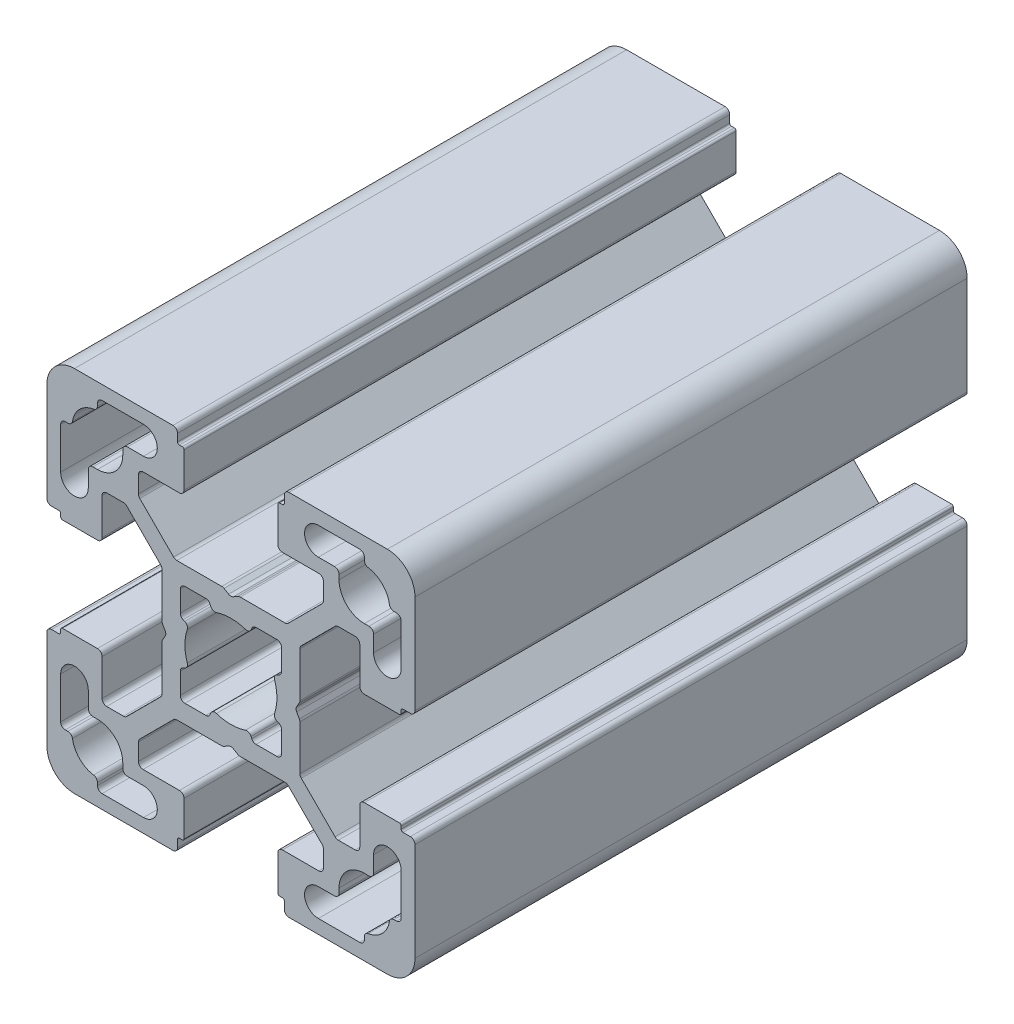
SolidWorks part; units mm, degrees
material "1060 Сплав"
ref_plane "Спереди" through (0, 0, 0) normal (0, 0, 1) x (1, 0, 0)
ref_plane "Сверху" through (0, 0, 0) normal (0, 1, 0) x (1, 0, 0)
ref_plane "Справа" through (0, 0, 0) normal (1, 0, 0) x (0, 0, -1)
sketch "Эскиз1" plane through (0, 0, 0) normal (0, 0, 1) x (1, 0, 0)
  line L0 (-14.5, 18) -> (-14.5, 17.7113)
  line L1 (-18.5, -5.6) -> (-18.5, -5.3)
  line L3 (-14, 18.5) -> (-9.5, 18.5)
  line L4 (18.5, 5.6) -> (18.5, 5.3)
  line L5 (0.25, 7.1443) -> (0.75, 7.433)
  line L6 (1, 7.5) -> (5.8787, 7.5)
  line L7 (5.6, 14) -> (5.6255, 13.9844)
  line L8 (-0.25, 7.1443) -> (-0.75, 7.433)
  line L9 (-5.8787, 7.5) -> (-1, 7.5)
  line L10 (-7.5, 5.8787) -> (-7.5, 1)
  line L11 (-5.6, 18.5) -> (-5.3, 18.5)
  line L12 (10.05, 13.5) -> (10.05, 11.6713)
  line L13 (-14, 5.6) -> (-13.9844, 5.6255)
  line L14 (-13.5, 10.05) -> (-11.6713, 10.05)
  line L15 (-5.1994, 2.2693) -> (-5.0205, 2.1915)
  line L16 (-19.5, 5.8) -> (-18.7, 5.8)
  line L17 (-18.3, 5.1) -> (-14.5, 5.1)
  line L18 (-14, 9.55) -> (-14, 5.6)
  line L19 (-7.6464, 6.2322) -> (-11.3178, 9.9036)
  line L20 (-20, 6.3) -> (-20, 17)
  line L21 (5.1994, -2.2693) -> (5.0205, -2.1915)
  line L22 (-14.5, 18) -> (-14.5, 17.7113)
  line L23 (-14, 18.5) -> (-9.5, 18.5)
  line L24 (-9.5, 15.5) -> (-11.25, 15.5)
  line L25 (-11.75, 15) -> (-11.75, 14.5)
  line L26 (-15, 11.75) -> (-14.5, 11.75)
  line L27 (-15.5, 9.5) -> (-15.5, 11.25)
  line L28 (-18.5, 14) -> (-18.5, 9.5)
  line L29 (-18, 14.5) -> (-17.7113, 14.5)
  line L30 (2.7278, -5.5) -> (5, -5.5)
  line L31 (-2.7278, 5.5) -> (-5, 5.5)
  line L32 (-5.5, 2.7278) -> (-5.5, 5)
  line L33 (5.8, 19.5) -> (5.8, 18.7)
  line L34 (5.1, 18.3) -> (5.1, 14.5)
  line L35 (-2.2693, 5.1994) -> (-2.1915, 5.0205)
  line L36 (9.55, 14) -> (5.6, 14)
  line L37 (-9.5, 15.5) -> (-11.25, 15.5)
  line L38 (2.2693, 5.1994) -> (2.1915, 5.0205)
  line L39 (5.5, 2.7278) -> (5.5, 5)
  line L40 (2.7278, 5.5) -> (5, 5.5)
  line L41 (5.1994, 2.2693) -> (5.0205, 2.1915)
  line L42 (5.5, -2.7278) -> (5.5, -5)
  line L43 (2.2693, -5.1994) -> (2.1915, -5.0205)
  line L44 (-2.2693, -5.1994) -> (-2.1915, -5.0205)
  line L45 (-5.5, -2.7278) -> (-5.5, -5)
  line L46 (-2.7278, -5.5) -> (-5, -5.5)
  line L47 (-5.1994, -2.2693) -> (-5.0205, -2.1915)
  line L48 (-7.1443, 0.25) -> (-7.433, 0.75)
  line L49 (-7.5, -1) -> (-7.5, -5.8787)
  line L50 (-7.1443, -0.25) -> (-7.433, -0.75)
  line L51 (-11.75, 15) -> (-11.75, 14.5)
  line L52 (-15, 11.75) -> (-14.5, 11.75)
  line L53 (-15.5, 9.5) -> (-15.5, 11.25)
  line L54 (-6.3, 20) -> (-17, 20)
  line L55 (-6.2322, 7.6464) -> (-9.9036, 11.3178)
  line L56 (-9.55, 14) -> (-5.6, 14)
  line L57 (-5.1, 18.3) -> (-5.1, 14.5)
  line L58 (-5.8, 19.5) -> (-5.8, 18.7)
  line L59 (-10.05, 13.5) -> (-10.05, 11.6713)
  line L60 (-5.6, 14) -> (-5.6255, 13.9844)
  line L61 (6.2322, 7.6464) -> (9.9036, 11.3178)
  line L62 (6.2322, 7.6464) -> (9.9036, 11.3178)
  line L63 (6.3, 20) -> (17, 20)
  line L64 (15.5, 9.5) -> (15.5, 11.25)
  line L65 (15, 11.75) -> (14.5, 11.75)
  line L66 (11.75, 15) -> (11.75, 14.5)
  line L67 (7.1443, -0.25) -> (7.433, -0.75)
  line L68 (7.5, -1) -> (7.5, -5.8787)
  line L69 (7.1443, 0.25) -> (7.433, 0.75)
  line L70 (5.1994, -2.2693) -> (5.0205, -2.1915)
  line L71 (2.7278, -5.5) -> (5, -5.5)
  line L72 (5.5, -2.7278) -> (5.5, -5)
  line L73 (2.2693, -5.1994) -> (2.1915, -5.0205)
  line L74 (9.5, 15.5) -> (11.25, 15.5)
  line L75 (2.2693, 5.1994) -> (2.1915, 5.0205)
  line L76 (5.5, 2.7278) -> (5.5, 5)
  line L77 (2.7278, 5.5) -> (5, 5.5)
  line L78 (18, 14.5) -> (17.7113, 14.5)
  line L79 (18.5, 14) -> (18.5, 9.5)
  line L80 (15.5, 9.5) -> (15.5, 11.25)
  line L81 (15, 11.75) -> (14.5, 11.75)
  line L82 (11.75, 15) -> (11.75, 14.5)
  line L83 (9.5, 15.5) -> (11.25, 15.5)
  line L84 (14, 18.5) -> (9.5, 18.5)
  line L85 (14.5, 18) -> (14.5, 17.7113)
  line L86 (20, 6.3) -> (20, 17)
  line L87 (7.6464, 6.2322) -> (11.3178, 9.9036)
  line L88 (7.6464, 6.2322) -> (11.3178, 9.9036)
  line L89 (14, 9.55) -> (14, 5.6)
  line L90 (18.3, 5.1) -> (14.5, 5.1)
  line L91 (5.1994, 2.2693) -> (5.0205, 2.1915)
  line L92 (19.5, 5.8) -> (18.7, 5.8)
  line L93 (13.5, 10.05) -> (11.6713, 10.05)
  line L94 (7.5, 5.8787) -> (7.5, 1)
  line L95 (14, 5.6) -> (13.9844, 5.6255)
  line L96 (5.6, 18.5) -> (5.3, 18.5)
  line L97 (5.1994, -2.2693) -> (5.0205, -2.1915)
  line L98 (14, 18.5) -> (9.5, 18.5)
  line L99 (14.5, 18) -> (14.5, 17.7113)
  line L100 (14.5, -18) -> (14.5, -17.7113)
  line L101 (7.6464, -6.2322) -> (11.3178, -9.9036)
  line L102 (14, -18.5) -> (9.5, -18.5)
  line L103 (5.6, -18.5) -> (5.3, -18.5)
  line L104 (14, -5.6) -> (13.9844, -5.6255)
  line L105 (13.5, -10.05) -> (11.6713, -10.05)
  line L106 (19.5, -5.8) -> (18.7, -5.8)
  line L107 (5.1994, -2.2693) -> (5.0205, -2.1915)
  line L108 (18.3, -5.1) -> (14.5, -5.1)
  line L109 (14, -9.55) -> (14, -5.6)
  line L110 (7.6464, -6.2322) -> (11.3178, -9.9036)
  line L111 (2.7278, -5.5) -> (5, -5.5)
  line L112 (5.5, -2.7278) -> (5.5, -5)
  line L113 (2.2693, -5.1994) -> (2.1915, -5.0205)
  line L114 (7.6464, -6.2322) -> (11.3178, -9.9036)
  line L115 (20, -6.3) -> (20, -17)
  line L116 (14.5, -18) -> (14.5, -17.7113)
  line L117 (14, -18.5) -> (9.5, -18.5)
  line L118 (9.5, -15.5) -> (11.25, -15.5)
  line L119 (6.2322, -7.6464) -> (9.9036, -11.3178)
  line L120 (11.75, -15) -> (11.75, -14.5)
  line L121 (15, -11.75) -> (14.5, -11.75)
  line L122 (15.5, -9.5) -> (15.5, -11.25)
  line L123 (18.5, -14) -> (18.5, -9.5)
  line L124 (18, -14.5) -> (17.7113, -14.5)
  line L125 (2.7278, -5.5) -> (5, -5.5)
  line L126 (-6.2322, -7.6464) -> (-9.9036, -11.3178)
  line L127 (5.5, -2.7278) -> (5.5, -5)
  line L128 (2.2693, -5.1994) -> (2.1915, -5.0205)
  line L129 (9.5, -15.5) -> (11.25, -15.5)
  line L130 (11.75, -15) -> (11.75, -14.5)
  line L131 (5.1994, -2.2693) -> (5.0205, -2.1915)
  line L132 (2.7278, -5.5) -> (5, -5.5)
  line L133 (5.5, -2.7278) -> (5.5, -5)
  line L134 (2.2693, -5.1994) -> (2.1915, -5.0205)
  line L135 (15, -11.75) -> (14.5, -11.75)
  line L136 (-2.2693, -5.1994) -> (-2.1915, -5.0205)
  line L137 (15.5, -9.5) -> (15.5, -11.25)
  line L138 (6.3, -20) -> (17, -20)
  line L139 (-5.5, -2.7278) -> (-5.5, -5)
  line L140 (-2.7278, -5.5) -> (-5, -5.5)
  line L141 (6.2322, -7.6464) -> (9.9036, -11.3178)
  line L142 (6.2322, -7.6464) -> (9.9036, -11.3178)
  line L143 (-5.6, -14) -> (-5.6255, -13.9844)
  line L144 (-10.05, -13.5) -> (-10.05, -11.6713)
  line L145 (-5.8, -19.5) -> (-5.8, -18.7)
  line L146 (-5.1, -18.3) -> (-5.1, -14.5)
  line L147 (-9.55, -14) -> (-5.6, -14)
  line L148 (-6.2322, -7.6464) -> (-9.9036, -11.3178)
  line L149 (-6.3, -20) -> (-17, -20)
  line L150 (-7.6464, -6.2322) -> (-11.3178, -9.9036)
  line L151 (-15.5, -9.5) -> (-15.5, -11.25)
  line L152 (-15, -11.75) -> (-14.5, -11.75)
  line L153 (-11.75, -15) -> (-11.75, -14.5)
  line L154 (-5.1994, -2.2693) -> (-5.0205, -2.1915)
  line L155 (-13.5, -10.05) -> (-11.6713, -10.05)
  line L156 (5.1994, -2.2693) -> (5.0205, -2.1915)
  line L157 (2.7278, -5.5) -> (5, -5.5)
  line L158 (-5.8787, -7.5) -> (-1, -7.5)
  line L159 (-0.25, -7.1443) -> (-0.75, -7.433)
  line L160 (5.5, -2.7278) -> (5.5, -5)
  line L161 (1, -7.5) -> (5.8787, -7.5)
  line L162 (0.25, -7.1443) -> (0.75, -7.433)
  line L163 (2.2693, -5.1994) -> (2.1915, -5.0205)
  line L164 (-9.5, -15.5) -> (-11.25, -15.5)
  line L165 (9.55, -14) -> (5.6, -14)
  line L166 (-18.5, 5.6) -> (-18.5, 5.3)
  line L167 (-2.2693, -5.1994) -> (-2.1915, -5.0205)
  line L168 (5.1, -18.3) -> (5.1, -14.5)
  line L169 (5.8, -19.5) -> (5.8, -18.7)
  line L170 (-5.5, -2.7278) -> (-5.5, -5)
  line L171 (-2.7278, -5.5) -> (-5, -5.5)
  line L172 (-18, -14.5) -> (-17.7113, -14.5)
  line L173 (-18.5, -14) -> (-18.5, -9.5)
  line L174 (-15.5, -9.5) -> (-15.5, -11.25)
  line L175 (-15, -11.75) -> (-14.5, -11.75)
  line L176 (-11.75, -15) -> (-11.75, -14.5)
  line L177 (-9.5, -15.5) -> (-11.25, -15.5)
  line L178 (-14, -18.5) -> (-9.5, -18.5)
  line L179 (-14.5, -18) -> (-14.5, -17.7113)
  line L180 (-20, -6.3) -> (-20, -17)
  line L181 (-7.6464, -6.2322) -> (-11.3178, -9.9036)
  line L182 (-14, -9.55) -> (-14, -5.6)
  line L183 (-18.3, -5.1) -> (-14.5, -5.1)
  line L184 (-19.5, -5.8) -> (-18.7, -5.8)
  line L185 (-5.1994, -2.2693) -> (-5.0205, -2.1915)
  line L186 (-13.5, -10.05) -> (-11.6713, -10.05)
  line L187 (-14, -5.6) -> (-13.9844, -5.6255)
  line L188 (10.05, -13.5) -> (10.05, -11.6713)
  line L189 (-5.6, -18.5) -> (-5.3, -18.5)
  line L190 (-5.8787, -7.5) -> (-1, -7.5)
  line L191 (-0.25, -7.1443) -> (-0.75, -7.433)
  line L192 (5.6, -14) -> (5.6255, -13.9844)
  line L193 (1, -7.5) -> (5.8787, -7.5)
  line L194 (0.25, -7.1443) -> (0.75, -7.433)
  line L195 (18.5, -5.6) -> (18.5, -5.3)
  line L196 (-14, -18.5) -> (-9.5, -18.5)
  line L197 (-14.5, -18) -> (-14.5, -17.7113)
  arc A0 (-17, 20) -> (-20, 17) centre (-17, 17) ccw
  arc A1 (-4.7453, 1.5754) -> (-4.7453, -1.5754) centre (0, 0) ccw
  arc A2 (-9.5, 15.5) -> (-9.5, 18.5) centre (-9.5, 17) ccw
  arc A3 (-14.9231, 17.2173) -> (-17.2173, 14.9231) centre (-14.5, 14.5) ccw
  arc A4 (-14.5, 11.75) -> (-11.75, 14.5) centre (-14.5, 14.5) ccw
  arc A5 (-15.5, 9.5) -> (-18.5, 9.5) centre (-17, 9.5) cw
  arc A6 (-11.3178, 9.9036) -> (-11.6713, 10.05) centre (-11.6713, 9.55) ccw
  arc A7 (-13.5, 10.05) -> (-14, 9.55) centre (-13.5, 9.55) ccw
  arc A8 (-14.5, 5.1) -> (-14, 5.6) centre (-14.5, 5.6) ccw
  arc A9 (-20, 6.3) -> (-19.5, 5.8) centre (-19.5, 6.3) ccw
  arc A10 (-11.25, 15.5) -> (-11.75, 15) centre (-11.25, 15) ccw
  arc A11 (-18.3, 5.1) -> (-18.5, 5.3) centre (-18.3, 5.3) cw
  arc A12 (-18.7, 5.8) -> (-18.5, 5.6) centre (-18.7, 5.6) cw
  arc A13 (-7.6464, 6.2322) -> (-7.5, 5.8787) centre (-8, 5.8787) cw
  arc A14 (-15, 11.75) -> (-15.5, 11.25) centre (-15, 11.25) ccw
  arc A15 (-14.5, 18) -> (-14, 18.5) centre (-14, 18) cw
  arc A16 (-18.5, 14) -> (-18, 14.5) centre (-18, 14) cw
  arc A17 (-14.5, 17.7113) -> (-14.9231, 17.2173) centre (-15, 17.7113) cw
  arc A18 (-17.7113, 14.5) -> (-17.2173, 14.9231) centre (-17.7113, 15) ccw
  arc A19 (-5.0205, 2.1915) -> (-4.7453, 1.5754) centre (-5.2198, 1.733) cw
  arc A20 (-2.1915, 5.0205) -> (-1.5754, 4.7453) centre (-1.733, 5.2198) ccw
  arc A21 (-2.2693, 5.1994) -> (-2.7278, 5.5) centre (-2.7278, 5) ccw
  arc A22 (-5, 5.5) -> (-5.5, 5) centre (-5, 5) ccw
  arc A23 (-5.1994, 2.2693) -> (-5.5, 2.7278) centre (-5, 2.7278) cw
  arc A24 (5.1994, 2.2693) -> (5.5, 2.7278) centre (5, 2.7278) ccw
  arc A25 (5, 5.5) -> (5.5, 5) centre (5, 5) cw
  arc A26 (2.2693, 5.1994) -> (2.7278, 5.5) centre (2.7278, 5) cw
  arc A27 (2.1915, 5.0205) -> (1.5754, 4.7453) centre (1.733, 5.2198) cw
  arc A28 (5.0205, 2.1915) -> (4.7453, 1.5754) centre (5.2198, 1.733) ccw
  arc A29 (5.0205, -2.1915) -> (4.7453, -1.5754) centre (5.2198, -1.733) cw
  arc A30 (2.1915, -5.0205) -> (1.5754, -4.7453) centre (1.733, -5.2198) ccw
  arc A31 (2.2693, -5.1994) -> (2.7278, -5.5) centre (2.7278, -5) ccw
  arc A32 (5, -5.5) -> (5.5, -5) centre (5, -5) ccw
  arc A33 (5.1994, -2.2693) -> (5.5, -2.7278) centre (5, -2.7278) cw
  arc A34 (-5.1994, -2.2693) -> (-5.5, -2.7278) centre (-5, -2.7278) ccw
  arc A35 (-5, -5.5) -> (-5.5, -5) centre (-5, -5) cw
  arc A36 (-2.2693, -5.1994) -> (-2.7278, -5.5) centre (-2.7278, -5) cw
  arc A37 (-2.1915, -5.0205) -> (-1.5754, -4.7453) centre (-1.733, -5.2198) cw
  arc A38 (-5.0205, -2.1915) -> (-4.7453, -1.5754) centre (-5.2198, -1.733) ccw
  arc A39 (1.5754, 4.7453) -> (-1.5754, 4.7453) centre (0, 0) ccw
  arc A40 (4.7453, -1.5754) -> (4.7453, 1.5754) centre (0, 0) ccw
  arc A41 (-1.5754, -4.7453) -> (1.5754, -4.7453) centre (0, 0) ccw
  arc A42 (-7.433, -0.75) -> (-7.5, -1) centre (-7, -1) ccw
  arc A43 (-7.1443, -0.25) -> (-7.1443, 0.25) centre (-7.5774, 0) ccw
  arc A44 (-7.433, 0.75) -> (-7.5, 1) centre (-7, 1) cw
  arc A45 (-14.5, 17.7113) -> (-14.9231, 17.2173) centre (-15, 17.7113) cw
  arc A46 (-17.7113, 14.5) -> (-17.2173, 14.9231) centre (-17.7113, 15) ccw
  arc A47 (-14, 18.5) -> (-14.5, 18) centre (-14, 18) ccw
  arc A48 (-11.75, 15) -> (-11.25, 15.5) centre (-11.25, 15) cw
  arc A49 (-6.2322, 7.6464) -> (-5.8787, 7.5) centre (-5.8787, 8) ccw
  arc A50 (-5.8, 18.7) -> (-5.6, 18.5) centre (-5.6, 18.7) ccw
  arc A51 (-5.1, 18.3) -> (-5.3, 18.5) centre (-5.3, 18.3) ccw
  arc A52 (-15.5, 11.25) -> (-15, 11.75) centre (-15, 11.25) cw
  arc A53 (-6.3, 20) -> (-5.8, 19.5) centre (-6.3, 19.5) cw
  arc A54 (-5.1, 14.5) -> (-5.6, 14) centre (-5.6, 14.5) cw
  arc A55 (-10.05, 13.5) -> (-9.55, 14) centre (-9.55, 13.5) cw
  arc A56 (-9.9036, 11.3178) -> (-10.05, 11.6713) centre (-9.55, 11.6713) cw
  arc A57 (-9.5, 15.5) -> (-9.5, 18.5) centre (-9.5, 17) ccw
  arc A58 (-15.5, 9.5) -> (-18.5, 9.5) centre (-17, 9.5) cw
  arc A59 (-0.75, 7.433) -> (-1, 7.5) centre (-1, 7) ccw
  arc A60 (0.25, 7.1443) -> (-0.25, 7.1443) centre (0, 7.5774) cw
  arc A61 (0.75, 7.433) -> (1, 7.5) centre (1, 7) cw
  arc A62 (15.5, 9.5) -> (18.5, 9.5) centre (17, 9.5) ccw
  arc A63 (9.5, 15.5) -> (9.5, 18.5) centre (9.5, 17) cw
  arc A64 (9.9036, 11.3178) -> (10.05, 11.6713) centre (9.55, 11.6713) ccw
  arc A65 (9.9036, 11.3178) -> (10.05, 11.6713) centre (9.55, 11.6713) ccw
  arc A66 (10.05, 13.5) -> (9.55, 14) centre (9.55, 13.5) ccw
  arc A67 (5.1, 14.5) -> (5.6, 14) centre (5.6, 14.5) ccw
  arc A68 (6.3, 20) -> (5.8, 19.5) centre (6.3, 19.5) ccw
  arc A69 (15.5, 11.25) -> (15, 11.75) centre (15, 11.25) ccw
  arc A70 (5.1, 18.3) -> (5.3, 18.5) centre (5.3, 18.3) cw
  arc A71 (6.2322, 7.6464) -> (5.8787, 7.5) centre (5.8787, 8) cw
  arc A72 (5.8, 18.7) -> (5.6, 18.5) centre (5.6, 18.7) cw
  arc A73 (6.2322, 7.6464) -> (5.8787, 7.5) centre (5.8787, 8) cw
  arc A74 (11.75, 15) -> (11.25, 15.5) centre (11.25, 15) ccw
  arc A75 (14, 18.5) -> (14.5, 18) centre (14, 18) cw
  arc A76 (7.433, 0.75) -> (7.5, 1) centre (7, 1) ccw
  arc A77 (7.1443, -0.25) -> (7.1443, 0.25) centre (7.5774, 0) cw
  arc A78 (7.433, -0.75) -> (7.5, -1) centre (7, -1) cw
  arc A79 (5.0205, -2.1915) -> (4.7453, -1.5754) centre (5.2198, -1.733) cw
  arc A80 (2.2693, -5.1994) -> (2.7278, -5.5) centre (2.7278, -5) ccw
  arc A81 (5, -5.5) -> (5.5, -5) centre (5, -5) ccw
  arc A82 (5.1994, -2.2693) -> (5.5, -2.7278) centre (5, -2.7278) cw
  arc A83 (5.1994, 2.2693) -> (5.5, 2.7278) centre (5, 2.7278) ccw
  arc A84 (5, 5.5) -> (5.5, 5) centre (5, 5) cw
  arc A85 (2.2693, 5.1994) -> (2.7278, 5.5) centre (2.7278, 5) cw
  arc A86 (5.0205, 2.1915) -> (4.7453, 1.5754) centre (5.2198, 1.733) ccw
  arc A87 (17.7113, 14.5) -> (17.2173, 14.9231) centre (17.7113, 15) cw
  arc A88 (14.5, 17.7113) -> (14.9231, 17.2173) centre (15, 17.7113) ccw
  arc A89 (5, 5.5) -> (5.5, 5) centre (5, 5) cw
  arc A90 (17.7113, 14.5) -> (17.2173, 14.9231) centre (17.7113, 15) cw
  arc A91 (14.5, 17.7113) -> (14.9231, 17.2173) centre (15, 17.7113) ccw
  arc A92 (7.6464, 6.2322) -> (7.5, 5.8787) centre (8, 5.8787) ccw
  arc A93 (18.5, 14) -> (18, 14.5) centre (18, 14) ccw
  arc A94 (14.5, 18) -> (14, 18.5) centre (14, 18) ccw
  arc A95 (15, 11.75) -> (15.5, 11.25) centre (15, 11.25) cw
  arc A96 (7.6464, 6.2322) -> (7.5, 5.8787) centre (8, 5.8787) ccw
  arc A97 (18.7, 5.8) -> (18.5, 5.6) centre (18.7, 5.6) ccw
  arc A98 (18.3, 5.1) -> (18.5, 5.3) centre (18.3, 5.3) ccw
  arc A99 (11.3178, 9.9036) -> (11.6713, 10.05) centre (11.6713, 9.55) cw
  arc A100 (11.25, 15.5) -> (11.75, 15) centre (11.25, 15) cw
  arc A101 (20, 6.3) -> (19.5, 5.8) centre (19.5, 6.3) cw
  arc A102 (14.5, 5.1) -> (14, 5.6) centre (14.5, 5.6) cw
  arc A103 (13.5, 10.05) -> (14, 9.55) centre (13.5, 9.55) cw
  arc A104 (4.7453, 1.5754) -> (4.7453, -1.5754) centre (0, 0) cw
  arc A105 (11.3178, 9.9036) -> (11.6713, 10.05) centre (11.6713, 9.55) cw
  arc A106 (15.5, 9.5) -> (18.5, 9.5) centre (17, 9.5) ccw
  arc A107 (14.5, 11.75) -> (11.75, 14.5) centre (14.5, 14.5) cw
  arc A108 (14.9231, 17.2173) -> (17.2173, 14.9231) centre (14.5, 14.5) cw
  arc A109 (9.5, 15.5) -> (9.5, 18.5) centre (9.5, 17) cw
  arc A110 (17, 20) -> (20, 17) centre (17, 17) cw
  arc A111 (11.3178, -9.9036) -> (11.6713, -10.05) centre (11.6713, -9.55) ccw
  arc A112 (17, -20) -> (20, -17) centre (17, -17) ccw
  arc A113 (9.5, -15.5) -> (9.5, -18.5) centre (9.5, -17) ccw
  arc A114 (14.9231, -17.2173) -> (17.2173, -14.9231) centre (14.5, -14.5) ccw
  arc A115 (14.5, -11.75) -> (11.75, -14.5) centre (14.5, -14.5) ccw
  arc A116 (15.5, -9.5) -> (18.5, -9.5) centre (17, -9.5) cw
  arc A117 (11.3178, -9.9036) -> (11.6713, -10.05) centre (11.6713, -9.55) ccw
  arc A118 (7.6464, -6.2322) -> (7.5, -5.8787) centre (8, -5.8787) cw
  arc A119 (13.5, -10.05) -> (14, -9.55) centre (13.5, -9.55) ccw
  arc A120 (14.5, -5.1) -> (14, -5.6) centre (14.5, -5.6) ccw
  arc A121 (20, -6.3) -> (19.5, -5.8) centre (19.5, -6.3) ccw
  arc A122 (11.25, -15.5) -> (11.75, -15) centre (11.25, -15) ccw
  arc A123 (11.3178, -9.9036) -> (11.6713, -10.05) centre (11.6713, -9.55) ccw
  arc A124 (5.0205, -2.1915) -> (4.7453, -1.5754) centre (5.2198, -1.733) cw
  arc A125 (2.2693, -5.1994) -> (2.7278, -5.5) centre (2.7278, -5) ccw
  arc A126 (5, -5.5) -> (5.5, -5) centre (5, -5) ccw
  arc A127 (5.1994, -2.2693) -> (5.5, -2.7278) centre (5, -2.7278) cw
  arc A128 (18.3, -5.1) -> (18.5, -5.3) centre (18.3, -5.3) cw
  arc A129 (18.7, -5.8) -> (18.5, -5.6) centre (18.7, -5.6) cw
  arc A130 (7.6464, -6.2322) -> (7.5, -5.8787) centre (8, -5.8787) cw
  arc A131 (15, -11.75) -> (15.5, -11.25) centre (15, -11.25) ccw
  arc A132 (6.2322, -7.6464) -> (5.8787, -7.5) centre (5.8787, -8) ccw
  arc A133 (14.5, -18) -> (14, -18.5) centre (14, -18) cw
  arc A134 (18.5, -14) -> (18, -14.5) centre (18, -14) cw
  arc A135 (7.6464, -6.2322) -> (7.5, -5.8787) centre (8, -5.8787) cw
  arc A136 (14.5, -17.7113) -> (14.9231, -17.2173) centre (15, -17.7113) cw
  arc A137 (17.7113, -14.5) -> (17.2173, -14.9231) centre (17.7113, -15) ccw
  arc A138 (5, -5.5) -> (5.5, -5) centre (5, -5) ccw
  arc A139 (9.9036, -11.3178) -> (10.05, -11.6713) centre (9.55, -11.6713) cw
  arc A140 (14.5, -17.7113) -> (14.9231, -17.2173) centre (15, -17.7113) cw
  arc A141 (17.7113, -14.5) -> (17.2173, -14.9231) centre (17.7113, -15) ccw
  arc A142 (0.75, -7.433) -> (1, -7.5) centre (1, -7) ccw
  arc A143 (0.25, -7.1443) -> (-0.25, -7.1443) centre (0, -7.5774) ccw
  arc A144 (-0.75, -7.433) -> (-1, -7.5) centre (-1, -7) cw
  arc A145 (2.2693, -5.1994) -> (2.7278, -5.5) centre (2.7278, -5) ccw
  arc A146 (5, -5.5) -> (5.5, -5) centre (5, -5) ccw
  arc A147 (-9.9036, -11.3178) -> (-10.05, -11.6713) centre (-9.55, -11.6713) ccw
  arc A148 (5.1994, -2.2693) -> (5.5, -2.7278) centre (5, -2.7278) cw
  arc A149 (14, -18.5) -> (14.5, -18) centre (14, -18) ccw
  arc A150 (11.75, -15) -> (11.25, -15.5) centre (11.25, -15) cw
  arc A151 (6.2322, -7.6464) -> (5.8787, -7.5) centre (5.8787, -8) ccw
  arc A152 (5.8, -18.7) -> (5.6, -18.5) centre (5.6, -18.7) ccw
  arc A153 (6.2322, -7.6464) -> (5.8787, -7.5) centre (5.8787, -8) ccw
  arc A154 (-6.2322, -7.6464) -> (-5.8787, -7.5) centre (-5.8787, -8) cw
  arc A155 (5.1, -18.3) -> (5.3, -18.5) centre (5.3, -18.3) ccw
  arc A156 (15.5, -11.25) -> (15, -11.75) centre (15, -11.25) cw
  arc A157 (6.3, -20) -> (5.8, -19.5) centre (6.3, -19.5) cw
  arc A158 (5.1, -14.5) -> (5.6, -14) centre (5.6, -14.5) cw
  arc A159 (1.5754, -4.7453) -> (-1.5754, -4.7453) centre (0, 0) cw
  arc A160 (5.0205, -2.1915) -> (4.7453, -1.5754) centre (5.2198, -1.733) cw
  arc A161 (2.1915, -5.0205) -> (1.5754, -4.7453) centre (1.733, -5.2198) ccw
  arc A162 (2.2693, -5.1994) -> (2.7278, -5.5) centre (2.7278, -5) ccw
  arc A163 (5, -5.5) -> (5.5, -5) centre (5, -5) ccw
  arc A164 (5.1994, -2.2693) -> (5.5, -2.7278) centre (5, -2.7278) cw
  arc A165 (-5.1994, -2.2693) -> (-5.5, -2.7278) centre (-5, -2.7278) ccw
  arc A166 (-5, -5.5) -> (-5.5, -5) centre (-5, -5) cw
  arc A167 (-2.2693, -5.1994) -> (-2.7278, -5.5) centre (-2.7278, -5) cw
  arc A168 (-2.1915, -5.0205) -> (-1.5754, -4.7453) centre (-1.733, -5.2198) cw
  arc A169 (-5.0205, -2.1915) -> (-4.7453, -1.5754) centre (-5.2198, -1.733) ccw
  arc A170 (10.05, -13.5) -> (9.55, -14) centre (9.55, -13.5) cw
  arc A171 (9.9036, -11.3178) -> (10.05, -11.6713) centre (9.55, -11.6713) cw
  arc A172 (9.9036, -11.3178) -> (10.05, -11.6713) centre (9.55, -11.6713) cw
  arc A173 (9.5, -15.5) -> (9.5, -18.5) centre (9.5, -17) ccw
  arc A174 (15.5, -9.5) -> (18.5, -9.5) centre (17, -9.5) cw
  arc A175 (-7.6464, -6.2322) -> (-7.5, -5.8787) centre (-8, -5.8787) ccw
  arc A176 (0.75, -7.433) -> (1, -7.5) centre (1, -7) ccw
  arc A177 (0.25, -7.1443) -> (-0.25, -7.1443) centre (0, -7.5774) ccw
  arc A178 (-0.75, -7.433) -> (-1, -7.5) centre (-1, -7) cw
  arc A179 (-15.5, -9.5) -> (-18.5, -9.5) centre (-17, -9.5) ccw
  arc A180 (-9.5, -15.5) -> (-9.5, -18.5) centre (-9.5, -17) cw
  arc A181 (-9.9036, -11.3178) -> (-10.05, -11.6713) centre (-9.55, -11.6713) ccw
  arc A182 (-11.3178, -9.9036) -> (-11.6713, -10.05) centre (-11.6713, -9.55) cw
  arc A183 (-10.05, -13.5) -> (-9.55, -14) centre (-9.55, -13.5) ccw
  arc A184 (-5.1, -14.5) -> (-5.6, -14) centre (-5.6, -14.5) ccw
  arc A185 (-6.3, -20) -> (-5.8, -19.5) centre (-6.3, -19.5) ccw
  arc A186 (-15.5, -11.25) -> (-15, -11.75) centre (-15, -11.25) ccw
  arc A187 (-5.1, -18.3) -> (-5.3, -18.5) centre (-5.3, -18.3) cw
  arc A188 (-5.8, -18.7) -> (-5.6, -18.5) centre (-5.6, -18.7) cw
  arc A189 (-6.2322, -7.6464) -> (-5.8787, -7.5) centre (-5.8787, -8) cw
  arc A190 (-11.75, -15) -> (-11.25, -15.5) centre (-11.25, -15) ccw
  arc A191 (-14, -18.5) -> (-14.5, -18) centre (-14, -18) cw
  arc A192 (-17.7113, -14.5) -> (-17.2173, -14.9231) centre (-17.7113, -15) cw
  arc A193 (-14.5, -17.7113) -> (-14.9231, -17.2173) centre (-15, -17.7113) ccw
  arc A194 (1.5754, -4.7453) -> (-1.5754, -4.7453) centre (0, 0) cw
  arc A195 (2.1915, -5.0205) -> (1.5754, -4.7453) centre (1.733, -5.2198) ccw
  arc A196 (2.2693, -5.1994) -> (2.7278, -5.5) centre (2.7278, -5) ccw
  arc A197 (5, -5.5) -> (5.5, -5) centre (5, -5) ccw
  arc A198 (5.1994, -2.2693) -> (5.5, -2.7278) centre (5, -2.7278) cw
  arc A199 (-5.1994, -2.2693) -> (-5.5, -2.7278) centre (-5, -2.7278) ccw
  arc A200 (-5, -5.5) -> (-5.5, -5) centre (-5, -5) cw
  arc A201 (-2.2693, -5.1994) -> (-2.7278, -5.5) centre (-2.7278, -5) cw
  arc A202 (-2.1915, -5.0205) -> (-1.5754, -4.7453) centre (-1.733, -5.2198) cw
  arc A203 (-17.7113, -14.5) -> (-17.2173, -14.9231) centre (-17.7113, -15) cw
  arc A204 (-14.5, -17.7113) -> (-14.9231, -17.2173) centre (-15, -17.7113) ccw
  arc A205 (-18.5, -14) -> (-18, -14.5) centre (-18, -14) ccw
  arc A206 (-14.5, -18) -> (-14, -18.5) centre (-14, -18) ccw
  arc A207 (-15, -11.75) -> (-15.5, -11.25) centre (-15, -11.25) cw
  arc A208 (-7.6464, -6.2322) -> (-7.5, -5.8787) centre (-8, -5.8787) ccw
  arc A209 (-18.7, -5.8) -> (-18.5, -5.6) centre (-18.7, -5.6) ccw
  arc A210 (-18.3, -5.1) -> (-18.5, -5.3) centre (-18.3, -5.3) ccw
  arc A211 (-11.25, -15.5) -> (-11.75, -15) centre (-11.25, -15) cw
  arc A212 (-20, -6.3) -> (-19.5, -5.8) centre (-19.5, -6.3) cw
  arc A213 (-14.5, -5.1) -> (-14, -5.6) centre (-14.5, -5.6) cw
  arc A214 (-13.5, -10.05) -> (-14, -9.55) centre (-13.5, -9.55) cw
  arc A215 (-11.3178, -9.9036) -> (-11.6713, -10.05) centre (-11.6713, -9.55) cw
  arc A216 (-15.5, -9.5) -> (-18.5, -9.5) centre (-17, -9.5) ccw
  arc A217 (-14.5, -11.75) -> (-11.75, -14.5) centre (-14.5, -14.5) cw
  arc A218 (-14.9231, -17.2173) -> (-17.2173, -14.9231) centre (-14.5, -14.5) cw
  arc A219 (-9.5, -15.5) -> (-9.5, -18.5) centre (-9.5, -17) cw
  arc A220 (-17, -20) -> (-20, -17) centre (-17, -17) cw
  point P0 (0, 0)
  point P6 (0, 0)
  point P52 (-11.75, 15.5)
  point P57 (-20, 5.8)
  point P61 (-15.5, 11.75)
  point P64 (-14.5, 18.5)
  point P67 (-18.5, 14.5)
  point P70 (-14.5, 17.25)
  point P73 (-17.25, 14.5)
  point P87 (-2.4, 5.5)
  point P93 (-5.5, 2.4)
  point P111 (5.5, 2.4)
  point P112 (2.4, 5.5)
  point P143 (2.4, -5.5)
  point P144 (5.5, -2.4)
  point P145 (-5.5, -2.4)
  point P146 (-2.4, -5.5)
  point P175 (-5.8, 20)
  point P257 (5.8, 20)
  point P258 (17.25, 14.5)
  point P259 (14.5, 17.25)
  point P260 (18.5, 14.5)
  point P261 (14.5, 18.5)
  point P262 (15.5, 11.75)
  point P263 (20, 5.8)
  point P264 (11.75, 15.5)
  point P421 (11.75, -15.5)
  point P422 (20, -5.8)
  point P423 (15.5, -11.75)
  point P424 (14.5, -18.5)
  point P425 (18.5, -14.5)
  point P426 (14.5, -17.25)
  point P427 (17.25, -14.5)
  point P428 (5.8, -20)
  point P429 (-5.8, -20)
  point P430 (-17.25, -14.5)
  point P431 (-14.5, -17.25)
  point P432 (-18.5, -14.5)
  point P433 (-14.5, -18.5)
  point P434 (-15.5, -11.75)
  point P435 (-20, -5.8)
  point P436 (-11.75, -15.5)
extrude "Бобышка-Вытянуть1" add sketch "Эскиз1" along normal blind 60
